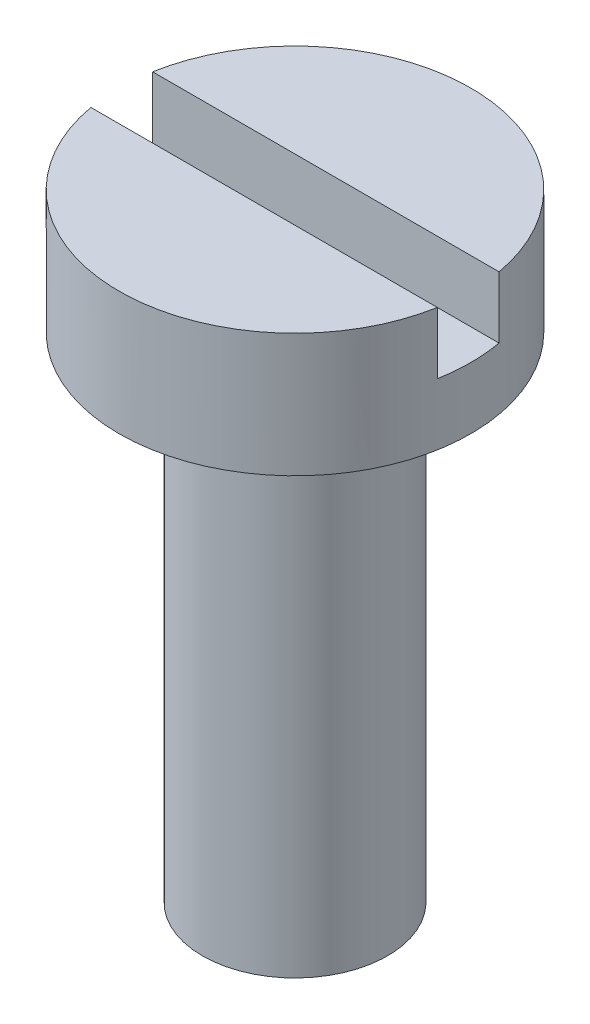
SolidWorks part; units mm, degrees
material "1023 Carbon Steel Sheet (SS)"
ref_plane "Front Plane" through (0, 0, 0) normal (0, 0, 1) x (1, 0, 0)
ref_plane "Top Plane" through (0, 0, 0) normal (0, 1, 0) x (1, 0, 0)
ref_plane "Right Plane" through (0, 0, 0) normal (1, 0, 0) x (0, 0, -1)
sketch "Sketch1" plane through (0, 0, 0) normal (0, 1, 0) x (1, 0, 0)
  circle A0 centre (0, 0) radius 2.85
  dimension "D1" = 5.7
extrude "Boss-Extrude1" add sketch "Sketch1" along normal blind 2
sketch "Sketch2" plane through (0, 0, 0) normal (0, 1, 0) x (1, 0, 0)
  circle A0 centre (0, 0) radius 1.5
  dimension "D1" = 3
extrude "Boss-Extrude2" add sketch "Sketch2" against normal blind 8
sketch "Sketch3" plane through (0, 2, 0) normal (0, 1, 0) x (1, 0, 0)
  line L1 (-3, -0.5) -> (3, -0.5)
  line L2 (-3, -0.5) -> (-3, 0.5)
  line L3 (-3, 0.5) -> (3, 0.5)
  line L4 (3, -0.5) -> (3, 0.5)
  line L5 (-3, -0.5) -> (3, 0.5) construction
  line L6 (-3, 0.5) -> (3, -0.5) construction
  point P0 (0, 0)
  dimension "D1" = 1
  dimension "D2" = 6
extrude "Cut-Extrude1" cut sketch "Sketch3" against normal blind 1
